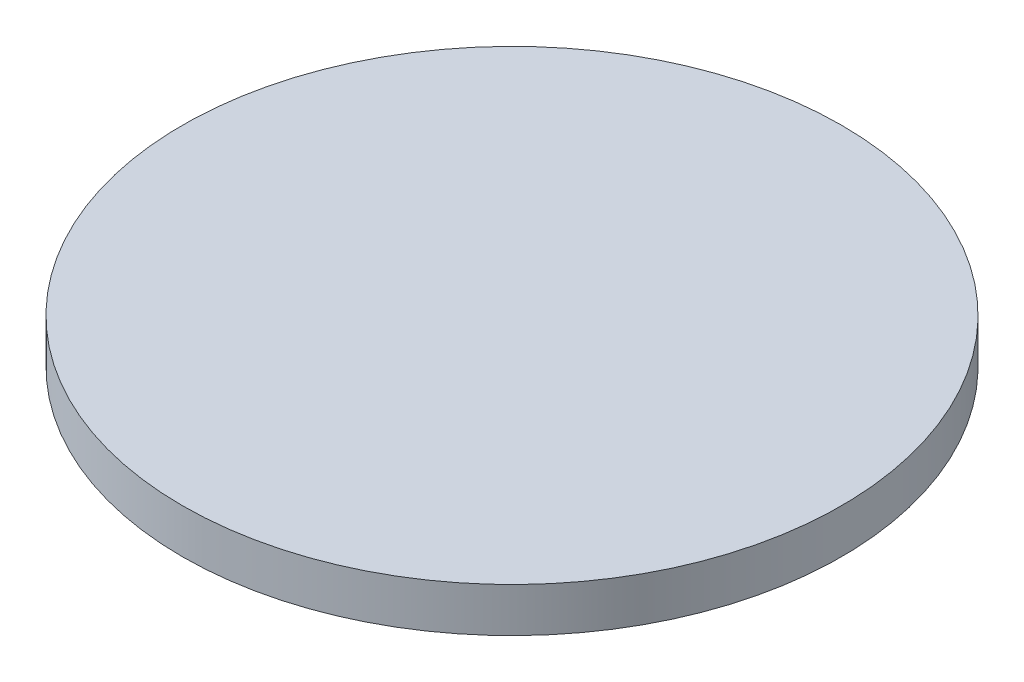
SolidWorks part; units mm, degrees
material "ABS"
ref_plane "Front Plane" through (0, 0, 0) normal (0, 0, 1) x (1, 0, 0)
ref_plane "Top Plane" through (0, 0, 0) normal (0, 1, 0) x (1, 0, 0)
ref_plane "Right Plane" through (0, 0, 0) normal (1, 0, 0) x (0, 0, -1)
sketch "Sketch1" plane through (0, 0, 0) normal (0, 1, 0) x (1, 0, 0)
  circle A0 centre (0, 0) radius 35
  dimension "D1" = 70
extrude "Boss-Extrude1" add sketch "Sketch1" along normal blind 4.7
